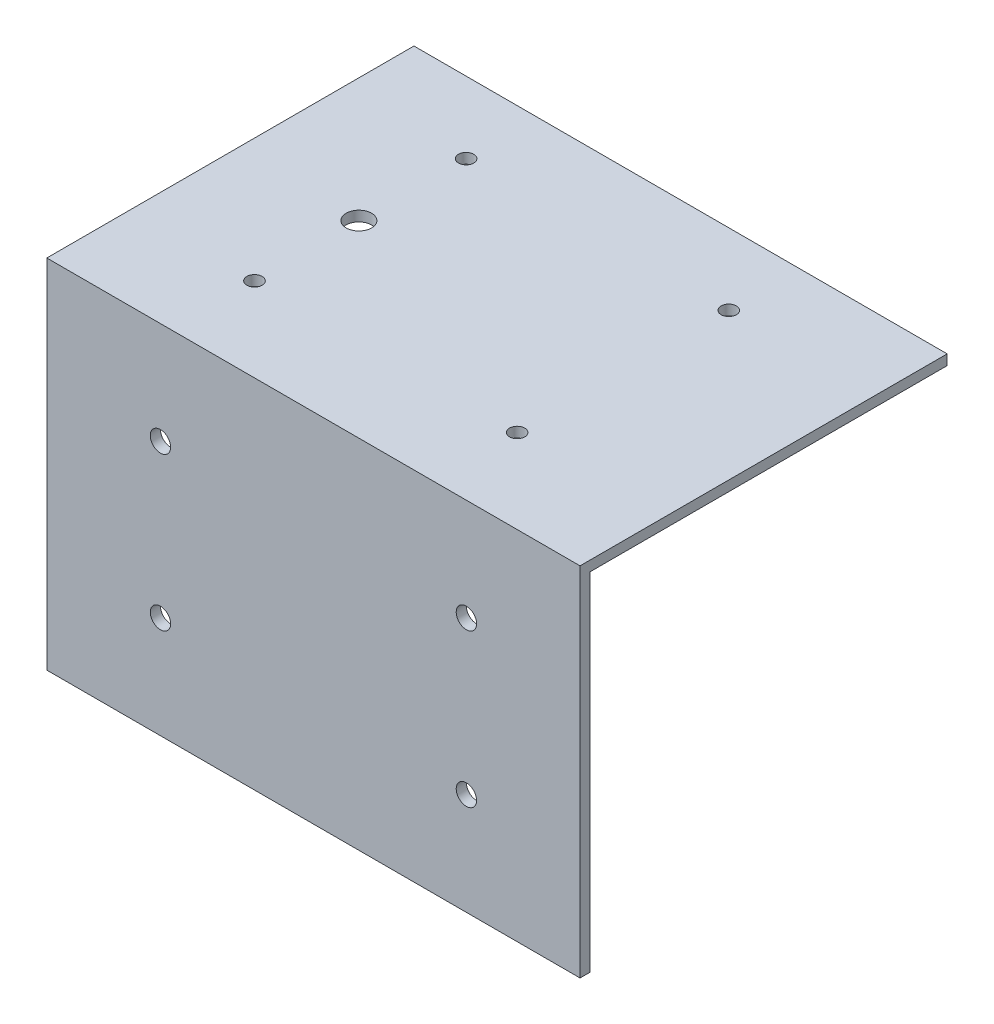
SolidWorks part; units mm, degrees
ref_plane "Front Plane" through (0, 0, 0) normal (0, 0, 1) x (1, 0, 0)
ref_plane "Top Plane" through (0, 0, 0) normal (0, 1, 0) x (1, 0, 0)
ref_plane "Right Plane" through (0, 0, 0) normal (1, 0, 0) x (0, 0, -1)
sketch "Sketch1" plane through (0, 0, 0) normal (0, 1, 0) x (1, 0, 0)
  line L0 (0, 35) -> (0, -18.7697) construction
  line L1 (-50, -35) -> (50, -35)
  line L2 (-50, -35) -> (-50, 35)
  line L3 (-50, 35) -> (50, 35)
  line L4 (50, -35) -> (50, 35)
  line L5 (-50, -35) -> (50, 35) construction
  line L6 (-50, 35) -> (50, -35) construction
  circle A0 centre (25.755, 20.98) radius 1.5
  circle A1 centre (-25.755, 20.98) radius 1.5
  circle A2 centre (25.755, -20.52) radius 1.5
  circle A3 centre (-25.755, -20.52) radius 1.5
  circle A4 centre (-25.755, -0.05) radius 2.5
  point P0 (0, 0)
  dimension "D7" = 3
  dimension "D8" = 3
  dimension "D9" = 3
  dimension "D10" = 3
  dimension "D11" = 5
  dimension "D1" = 100
  dimension "D2" = 70
  dimension "D3" = 51.51
  dimension "D4" = 25.755
  dimension "D5" = 41.5
  dimension "D6" = 41.5
  dimension "D12" = 21.03
  dimension "D13" = 14.02
extrude "Boss-Extrude1" add sketch "Sketch1" along normal blind 2
sketch "Sketch2" plane through (0, 2, 0) normal (0, 1, 0) x (1, 0, 0)
  line L1 (-50, -35) -> (20, -35)
  line L2 (-50, -35) -> (-50, -37)
  line L3 (-50, -37) -> (20, -37)
  line L4 (20, -35) -> (20, -37)
  dimension "D1" = 2
  dimension "D2" = 70
extrude "Boss-Extrude2" add sketch "Sketch2" against normal blind 70
sketch "Sketch3" plane through (50, 0, 0) normal (1, 0, 0) x (0, 0, -1)
  line L1 (35, 2) -> (-35, 2)
  line L2 (35, 2) -> (35, 0)
  line L3 (35, 0) -> (-35, 0)
  line L4 (-35, 2) -> (-35, 0)
extrude "Boss-Extrude3" add sketch "Sketch3" along normal blind 4.57
sketch "Sketch4" plane through (0, 2, 0) normal (0, 1, 0) x (1, 0, 0)
  line L1 (20, -35) -> (54.57, -35)
  line L2 (20, -35) -> (20, -37)
  line L3 (20, -37) -> (54.57, -37)
  line L4 (54.57, -35) -> (54.57, -37)
extrude "Boss-Extrude4" add sketch "Sketch4" against normal up to surface (70 mm away) up to face at (-15, -68, 36)
sketch "Sketch5" plane through (0, 0, 35) normal (0, 0, -1) x (-1, 0, 0)
  line L0 (-2.285, -68) -> (-2.285, 2) construction
  line L1 (-54.57, -68) -> (50, -68) construction
  line L2 (-54.57, 2) -> (50, 2) construction
  circle A0 centre (-32.285, -18) radius 2
  circle A2 centre (27.715, -48) radius 2
  circle A3 centre (-32.285, -48) radius 2
  circle A4 centre (27.715, -18) radius 2
  dimension "D1" = 4
  dimension "D2" = 4
  dimension "D3" = 4
  dimension "D4" = 4
  dimension "D5" = 20
  dimension "D6" = 20
  dimension "D7" = 30
  dimension "D8" = 30
  dimension "D9" = 30
  dimension "D10" = 30
extrude "Cut-Extrude1" cut sketch "Sketch5" against normal blind 10
